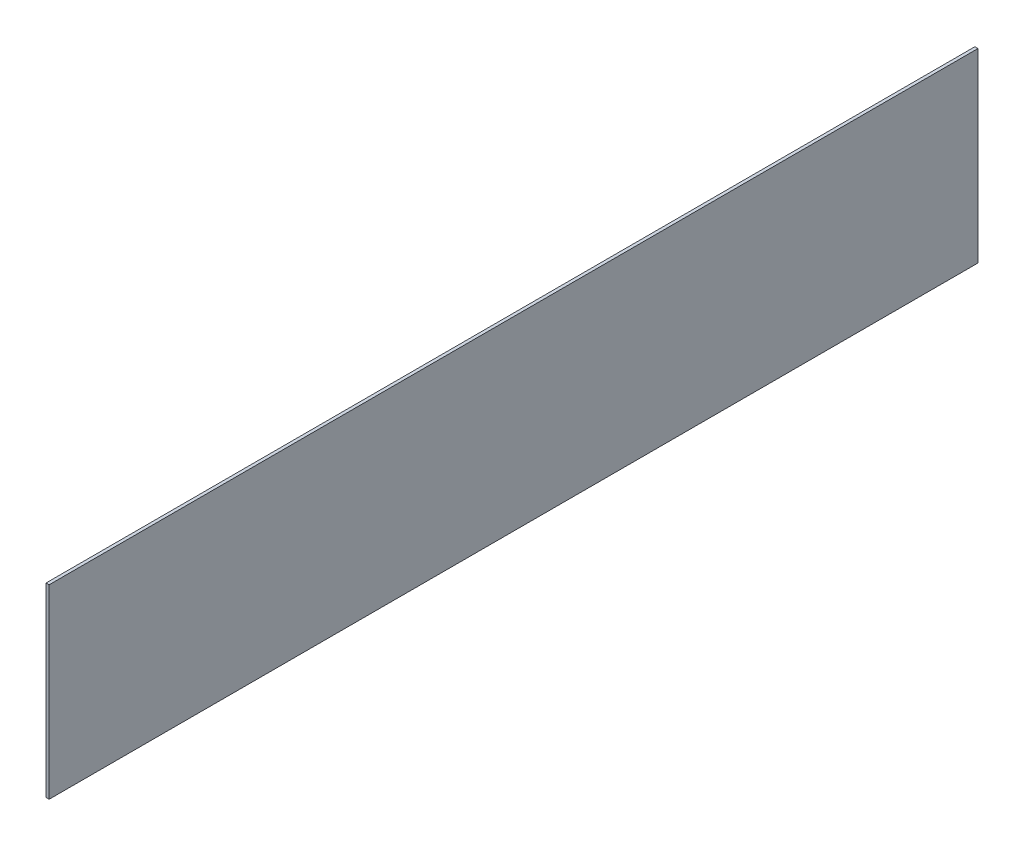
SolidWorks part; units mm, degrees
ref_plane "Ebene vorne" through (0, 0, 0) normal (0, 0, 1) x (1, 0, 0)
ref_plane "Ebene oben" through (0, 0, 0) normal (0, 1, 0) x (1, 0, 0)
ref_plane "Ebene rechts" through (0, 0, 0) normal (1, 0, 0) x (0, 0, -1)
sketch "Skizze1" plane through (0, 0, 0) normal (0, 0, 1) x (1, 0, 0)
  line L0 (0, 0) -> (0, 60)
  dimension "D1" = 60
extrude "Linear-Austragen-Dünn1" add sketch "Skizze1" along normal blind 300 thin
